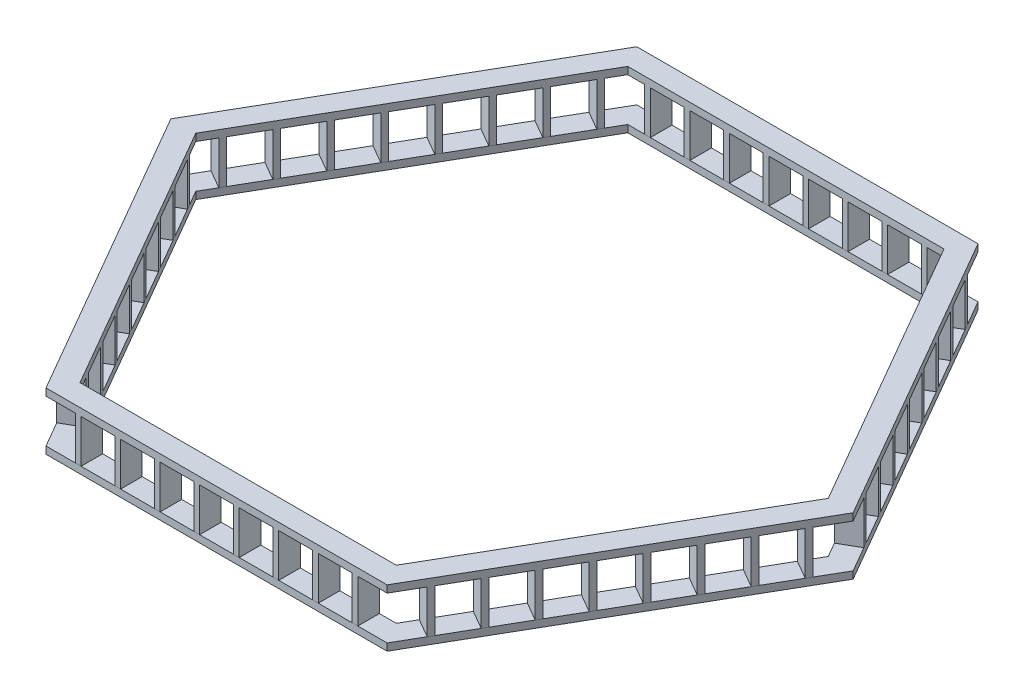
SolidWorks part; units mm, degrees
ref_plane "前视基准面" through (0, 0, 0) normal (0, 0, 1) x (1, 0, 0)
ref_plane "上视基准面" through (0, 0, 0) normal (0, 1, 0) x (1, 0, 0)
ref_plane "右视基准面" through (0, 0, 0) normal (1, 0, 0) x (0, 0, -1)
sketch "草图1" plane through (0, 0, 0) normal (0, 1, 0) x (1, 0, 0)
  line L0 (-1186.6025, -2055.2559) -> (1186.6025, -2055.2559)
  line L1 (-1100, -1905.2559) -> (1100, -1905.2559)
  line L2 (1100, -1905.2559) -> (2200, 0)
  line L3 (2200, 0) -> (1100, 1905.2559)
  line L4 (1100, 1905.2559) -> (-1100, 1905.2559)
  line L5 (-1100, 1905.2559) -> (-2200, 0)
  line L6 (-2200, 0) -> (-1100, -1905.2559)
  line L7 (1186.6025, -2055.2559) -> (2373.2051, 0)
  line L8 (2373.2051, 0) -> (1186.6025, 2055.2559)
  line L9 (1186.6025, 2055.2559) -> (-1186.6025, 2055.2559)
  line L10 (-1186.6025, 2055.2559) -> (-2373.2051, 0)
  line L11 (-2373.2051, 0) -> (-1186.6025, -2055.2559)
  circle A0 centre (0, 0) radius 1905.2559 construction
  dimension "D1" = 2200
  dimension "D2" = 150
extrude "凸台-拉伸2" add sketch "草图1" along normal blind 50
ref_plane "基准面2" through (0, 50, 0) normal (0, 1, 0) x (1, 0, 0)
sketch "草图2" plane through (0, 50, 0) normal (0, 1, 0) x (1, 0, 0)
  line L0 (0, 1905.2559) -> (0, 2055.2559) construction
  line L1 (1100, 1905.2559) -> (-1100, 1905.2559) construction
  line L2 (1186.6025, 2055.2559) -> (-1186.6025, 2055.2559) construction
  line L3 (-1100, 1905.2559) -> (-1100, 2055.2559) construction
  line L4 (1100, 1905.2559) -> (1100, 2055.2559) construction
  line L5 (0, 1905.2559) -> (-1100, 1905.2559) construction
  line L6 (-550, 1905.2559) -> (-550, 2055.2559) construction
  line L7 (-550, 2055.2559) -> (0, 2055.2559) construction
  line L8 (0, 1905.2559) -> (1100, 1905.2559) construction
  line L9 (550, 1905.2559) -> (550, 2055.2559) construction
  line L10 (0, 2055.2559) -> (550, 2055.2559) construction
  line L11 (550, 2055.2559) -> (1100, 2055.2559) construction
  line L12 (275, 2055.2559) -> (275, 1905.2559) construction
  line L13 (825, 2055.2559) -> (825, 1905.2559) construction
  line L14 (0, 2055.2559) -> (-550, 2055.2559) construction
  line L15 (-550, 2055.2559) -> (-1100, 2055.2559) construction
  line L16 (-825, 2055.2559) -> (-825, 1905.2559) construction
  line L17 (-275, 2055.2559) -> (-275, 1905.2559) construction
  line L18 (275, 2055.2559) -> (0, 2055.2559) construction
  line L19 (137.5, 2055.2559) -> (137.5, 1905.2559) construction
  line L20 (275, 2055.2559) -> (550, 2055.2559) construction
  line L21 (550, 2055.2559) -> (825, 2055.2559) construction
  line L22 (825, 2055.2559) -> (1100, 2055.2559) construction
  line L23 (412.5, 2055.2559) -> (412.5, 1905.2559) construction
  line L24 (687.5, 2055.2559) -> (687.5, 1905.2559) construction
  line L25 (962.5, 2055.2559) -> (962.5, 1905.2559) construction
  line L26 (0, 2055.2559) -> (-275, 2055.2559) construction
  line L27 (-275, 2055.2559) -> (-550, 2055.2559) construction
  line L28 (-550, 2055.2559) -> (-825, 2055.2559) construction
  line L29 (-825, 2055.2559) -> (-1100, 2055.2559) construction
  line L30 (-962.5, 2055.2559) -> (-962.5, 1905.2559) construction
  line L31 (-687.5, 2055.2559) -> (-687.5, 1905.2559) construction
  line L32 (-412.5, 2055.2559) -> (-412.5, 1905.2559) construction
  line L33 (-137.5, 2055.2559) -> (-137.5, 1905.2559) construction
  line L34 (117.5, 1905.2559) -> (117.5, 2055.2559)
  line L35 (117.5, 1905.2559) -> (157.5, 1905.2559)
  line L36 (117.5, 2055.2559) -> (157.5, 2055.2559)
  line L37 (157.5, 1905.2559) -> (157.5, 2055.2559)
  line L38 (117.5, 1905.2559) -> (157.5, 2055.2559) construction
  line L39 (117.5, 2055.2559) -> (157.5, 1905.2559) construction
  line L40 (432.5, 2055.2559) -> (392.5, 1905.2559) construction
  line L41 (432.5, 1905.2559) -> (392.5, 2055.2559) construction
  line L42 (432.5, 1905.2559) -> (392.5, 1905.2559)
  line L43 (432.5, 1905.2559) -> (432.5, 2055.2559)
  line L44 (432.5, 2055.2559) -> (392.5, 2055.2559)
  line L45 (392.5, 1905.2559) -> (392.5, 2055.2559)
  line L46 (667.5, 1905.2559) -> (707.5, 1905.2559)
  line L47 (667.5, 1905.2559) -> (707.5, 2055.2559) construction
  line L48 (667.5, 2055.2559) -> (707.5, 1905.2559) construction
  line L49 (667.5, 1905.2559) -> (667.5, 2055.2559)
  line L50 (707.5, 1905.2559) -> (707.5, 2055.2559)
  line L51 (667.5, 2055.2559) -> (707.5, 2055.2559)
  line L52 (982.5, 1905.2559) -> (942.5, 2055.2559) construction
  line L53 (982.5, 2055.2559) -> (942.5, 1905.2559) construction
  line L54 (982.5, 1905.2559) -> (942.5, 1905.2559)
  line L55 (982.5, 1905.2559) -> (982.5, 2055.2559)
  line L56 (982.5, 2055.2559) -> (942.5, 2055.2559)
  line L57 (942.5, 1905.2559) -> (942.5, 2055.2559)
  line L58 (-432.5, 1905.2559) -> (-432.5, 2055.2559)
  line L59 (-982.5, 2055.2559) -> (-942.5, 2055.2559)
  line L60 (-982.5, 1905.2559) -> (-942.5, 1905.2559)
  line L61 (-942.5, 1905.2559) -> (-942.5, 2055.2559)
  line L62 (-982.5, 1905.2559) -> (-982.5, 2055.2559)
  line L63 (-667.5, 1905.2559) -> (-707.5, 1905.2559)
  line L64 (-707.5, 1905.2559) -> (-707.5, 2055.2559)
  line L65 (-667.5, 2055.2559) -> (-707.5, 2055.2559)
  line L66 (-667.5, 1905.2559) -> (-667.5, 2055.2559)
  line L67 (-432.5, 1905.2559) -> (-392.5, 1905.2559)
  line L68 (-432.5, 2055.2559) -> (-392.5, 2055.2559)
  line L69 (-392.5, 1905.2559) -> (-392.5, 2055.2559)
  line L70 (-117.5, 1905.2559) -> (-157.5, 1905.2559)
  line L71 (-117.5, 1905.2559) -> (-117.5, 2055.2559)
  line L72 (-117.5, 2055.2559) -> (-157.5, 2055.2559)
  line L73 (-157.5, 1905.2559) -> (-157.5, 2055.2559)
  point P41 (137.5, 1980.2559)
  point P47 (137.5, 1980.2559)
  dimension "D1" = 40
extrude "凸台-拉伸3" add sketch "草图2" along normal blind 300 separate body
sketch "草图3" plane through (0, 0, 0) normal (0, 0, 1) x (1, 0, 0)
  line L0 (0, 0) -> (0, 600) construction
  dimension "D1" = 600
pattern_circular "阵列(圆周)2" count 6 every 60 about axis through (0, 0, 0) along (0, 1, 0) of bodies 171 169 173 174 172 108 168 170
ref_plane "基准面3" through (0, 350, 0) normal (0, 1, 0) x (1, 0, 0)
sketch "草图5" plane through (0, 350, 0) normal (0, 1, 0) x (1, 0, 0)
  line L0 (-2373.2051, 0) -> (-1186.6025, -2055.2559) construction
  line L1 (-2200, 0) -> (-1100, -1905.2559) construction
  line L2 (-1186.6025, -2055.2559) -> (1186.6025, -2055.2559) construction
  line L3 (-1100, -1905.2559) -> (1100, -1905.2559) construction
  line L4 (1100, -1905.2559) -> (2200, 0) construction
  line L5 (1186.6025, -2055.2559) -> (2373.2051, 0) construction
  line L6 (2373.2051, 0) -> (1186.6025, 2055.2559) construction
  line L7 (2200, 0) -> (1100, 1905.2559) construction
  line L8 (1100, 1905.2559) -> (-1100, 1905.2559) construction
  line L9 (1186.6025, 2055.2559) -> (-1186.6025, 2055.2559) construction
  line L10 (-1186.6025, 2055.2559) -> (-2373.2051, 0) construction
  line L11 (-1100, 1905.2559) -> (-2200, 0) construction
  line L12 (-2373.2051, 0) -> (-1186.6025, -2055.2559)
  line L13 (-2200, 0) -> (-1100, -1905.2559)
  line L14 (-1186.6025, -2055.2559) -> (1186.6025, -2055.2559)
  line L15 (-1100, -1905.2559) -> (1100, -1905.2559)
  line L16 (1100, -1905.2559) -> (2200, 0)
  line L17 (1186.6025, -2055.2559) -> (2373.2051, 0)
  line L18 (2373.2051, 0) -> (1186.6025, 2055.2559)
  line L19 (2200, 0) -> (1100, 1905.2559)
  line L20 (1100, 1905.2559) -> (-1100, 1905.2559)
  line L21 (1186.6025, 2055.2559) -> (-1186.6025, 2055.2559)
  line L22 (-1186.6025, 2055.2559) -> (-2373.2051, 0)
  line L23 (-1100, 1905.2559) -> (-2200, 0)
extrude "凸台-拉伸5" add sketch "草图5" along normal blind 50
